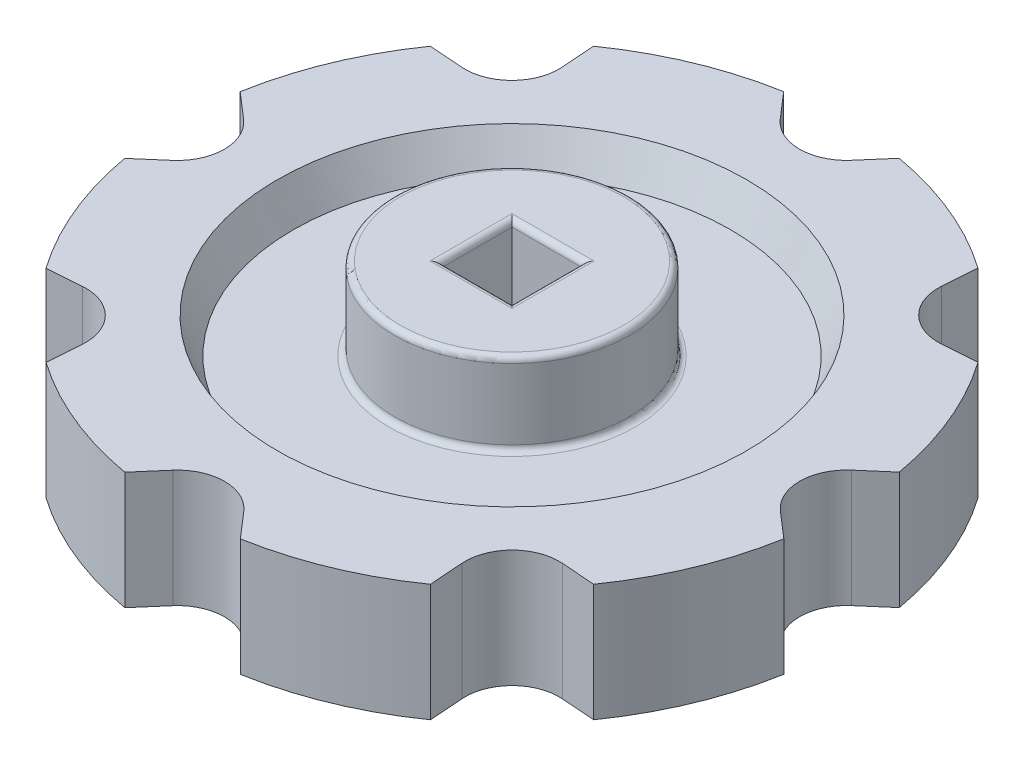
SolidWorks part; units mm, degrees
ref_plane "Спереди" through (0, 0, 0) normal (0, 0, 1) x (1, 0, 0)
ref_plane "Сверху" through (0, 0, 0) normal (0, 1, 0) x (1, 0, 0)
ref_plane "Справа" through (0, 0, 0) normal (1, 0, 0) x (0, 0, -1)
sketch "Эскиз1" plane through (0, 0, 0) normal (0, 0, 1) x (1, 0, 0)
  line L0 (0, 0) -> (0, 6.1755) construction
  line L1 (20, 2) -> (20, 7)
  line L2 (0, 0) -> (20, 0)
  line L3 (0, 0) -> (0, 4)
  line L4 (0, 4) -> (20, 4)
  line L5 (20, 0) -> (20, 4)
  line L6 (0, 4) -> (10, 4)
  line L7 (0, 4) -> (0, 11)
  line L8 (0, 11) -> (10, 11)
  line L9 (10, 4) -> (10, 11)
  line L10 (0, 0) -> (10, 0)
  line L11 (0, 0) -> (0, -1)
  line L12 (0, -1) -> (10, -1)
  line L13 (10, 0) -> (10, -1)
  line L14 (20, 7) -> (28.5, 7)
  line L15 (28.5, 7) -> (28.5, -3)
  line L16 (28.5, -3) -> (20, -3)
  line L17 (20, -3) -> (20, 0)
  line L18 (20, 7) -> (18.6252, 4)
  line L19 (20, -3) -> (18.6252, 0)
  dimension "D1" = 20
  dimension "D2" = 7
  dimension "D3" = 1
  dimension "D4" = 4
  dimension "D5" = 10
  dimension "D6" = 10
  dimension "D7" = 3
  dimension "D8" = 5
  dimension "D9" = 8.5
  dimension "D10" = 3.3
  dimension "D11" = 3.3
revolve "Повернуть1" add sketch "Эскиз1" angle 360 about L0
fillet "Скругление3" radius 0.5 1 edges at (0, 4, -10)
fillet "Скругление4" radius 0.5 1 edges at (0, 0, -10)
sketch "Эскиз4" plane through (0, 7, 0) normal (0, 1, 0) x (1, 0, 0)
  line L0 (-3.0327, 25.8838) -> (-8.7531, 32.4997)
  line L1 (-0.0069, 24.5) -> (-0.0069, 32.5) construction
  line L2 (3.0189, 25.8838) -> (8.7393, 32.4997)
  line L3 (-8.7531, 32.4997) -> (8.7393, 32.4997)
  line L4 (16.7914, 29.1701) -> (29.1604, 16.8011)
  line L5 (20.4373, 16.1679) -> (29.1604, 16.8011)
  line L6 (16.1582, 20.447) -> (16.7914, 29.1701)
  line L7 (32.4997, 8.7531) -> (32.4997, -8.7393)
  line L8 (25.8838, -3.0189) -> (32.4997, -8.7393)
  line L9 (25.8838, 3.0327) -> (32.4997, 8.7531)
  line L10 (29.1701, -16.7914) -> (16.8011, -29.1604)
  line L11 (16.1679, -20.4373) -> (16.8011, -29.1604)
  line L12 (20.447, -16.1582) -> (29.1701, -16.7914)
  line L13 (8.7531, -32.4997) -> (-8.7393, -32.4997)
  line L14 (-3.0189, -25.8838) -> (-8.7393, -32.4997)
  line L15 (3.0327, -25.8838) -> (8.7531, -32.4997)
  line L16 (-16.7914, -29.1701) -> (-29.1604, -16.8011)
  line L17 (-20.4373, -16.1679) -> (-29.1604, -16.8011)
  line L18 (-16.1582, -20.447) -> (-16.7914, -29.1701)
  line L19 (-32.4997, -8.7531) -> (-32.4997, 8.7393)
  line L20 (-25.8838, 3.0189) -> (-32.4997, 8.7393)
  line L21 (-25.8838, -3.0327) -> (-32.4997, -8.7531)
  line L22 (-29.1701, 16.7914) -> (-16.8011, 29.1604)
  line L23 (-16.1679, 20.4373) -> (-16.8011, 29.1604)
  line L24 (-20.447, 16.1582) -> (-29.1701, 16.7914)
  arc A0 (-3.0327, 25.8838) -> (3.0189, 25.8838) centre (-0.0069, 28.5) ccw
  arc A1 (16.1582, 20.447) -> (20.4373, 16.1679) centre (20.1477, 20.1574) ccw
  arc A2 (25.8838, 3.0327) -> (25.8838, -3.0189) centre (28.5, 0.0069) ccw
  arc A3 (20.447, -16.1582) -> (16.1679, -20.4373) centre (20.1574, -20.1477) ccw
  arc A4 (3.0327, -25.8838) -> (-3.0189, -25.8838) centre (0.0069, -28.5) ccw
  arc A5 (-16.1582, -20.447) -> (-20.4373, -16.1679) centre (-20.1477, -20.1574) ccw
  arc A6 (-25.8838, -3.0327) -> (-25.8838, 3.0189) centre (-28.5, -0.0069) ccw
  arc A7 (-20.447, 16.1582) -> (-16.1679, 20.4373) centre (-20.1574, 20.1477) ccw
  dimension "D1" = 8
  dimension "D2" = 28.5
  dimension "D3" = 8.746
  dimension "D4" = 81.696
  dimension "D5" = 8
extrude "Вырез-Вытянуть1" cut sketch "Эскиз4" against normal blind 10
sketch "Эскиз5" plane through (0, -1, 0) normal (0, -1, 0) x (1, 0, 0)
  line L1 (-3, -3) -> (3, -3)
  line L2 (-3, -3) -> (-3, 3)
  line L3 (-3, 3) -> (3, 3)
  line L4 (3, -3) -> (3, 3)
  line L5 (-3, -3) -> (3, 3) construction
  line L6 (-3, 3) -> (3, -3) construction
  point P0 (0, 0)
  dimension "D1" = 6
  dimension "D2" = 6
extrude "Вырез-Вытянуть2" cut sketch "Эскиз5" against normal up to next
fillet "Скругление5" radius 0.5 8 edges at (-3, 11, 0) (0, 11, 3) (3, 11, 0) (0, 11, -3) (0, -1, 3) (-3, -1, 0) (0, -1, -3) (3, -1, 0)
fillet "Скругление6" radius 0.5 1 edges at (0, 11, -10)
